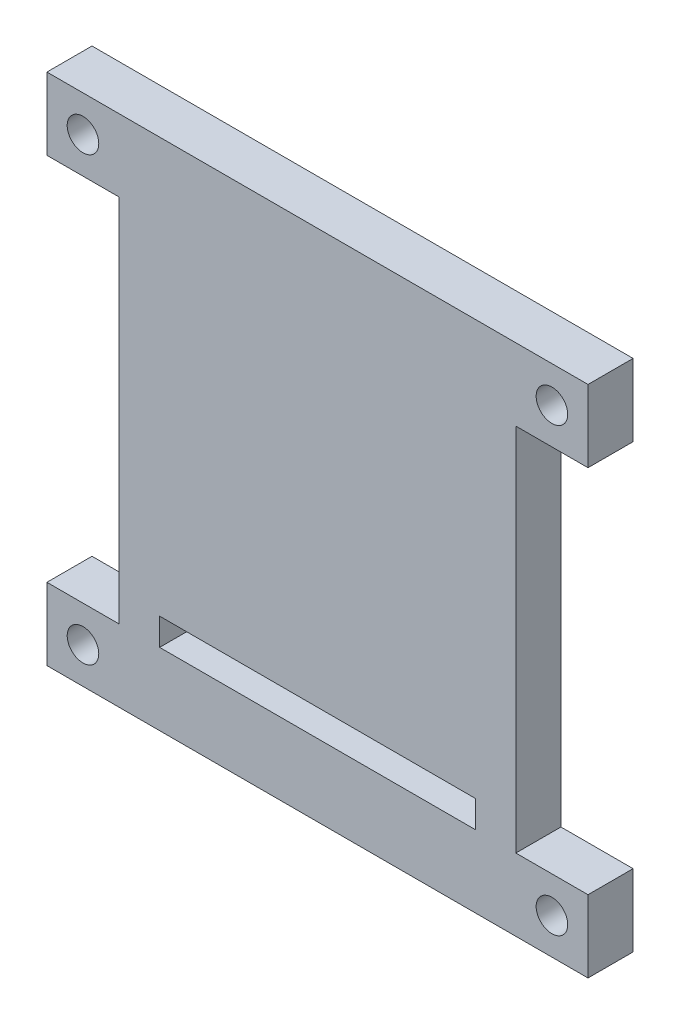
SolidWorks part; units mm, degrees
ref_plane "前基準面" through (0, 0, 0) normal (0, 0, 1) x (1, 0, 0)
ref_plane "上基準面" through (0, 0, 0) normal (0, 1, 0) x (1, 0, 0)
ref_plane "右基準面" through (0, 0, 0) normal (1, 0, 0) x (0, 0, -1)
sketch "草圖1" plane through (0, 0, 0) normal (0, 0, 1) x (1, 0, 0)
  line L1 (-22, 28.5) -> (22, 28.5)
  line L2 (-22, 28.5) -> (-22, -28.5)
  line L3 (-22, -28.5) -> (22, -28.5)
  line L4 (22, 28.5) -> (22, -28.5)
  line L5 (-22, 28.5) -> (22, -28.5) construction
  line L6 (-22, -28.5) -> (22, 28.5) construction
  line L7 (-30, 20.5) -> (-22, 20.5)
  line L8 (-30, 20.5) -> (-30, 28.5)
  line L9 (-30, 28.5) -> (-22, 28.5)
  line L10 (-22, 20.5) -> (-22, 28.5)
  line L11 (-30, 20.5) -> (-22, 28.5) construction
  line L12 (-30, 28.5) -> (-22, 20.5) construction
  line L13 (-30, -20.5) -> (-22, -20.5)
  line L14 (-30, -20.5) -> (-30, -28.5)
  line L15 (-30, -28.5) -> (-22, -28.5)
  line L16 (-22, -20.5) -> (-22, -28.5)
  line L17 (-30, -20.5) -> (-22, -28.5) construction
  line L18 (-30, -28.5) -> (-22, -20.5) construction
  line L19 (30, 20.5) -> (22, 20.5)
  line L20 (30, 20.5) -> (30, 28.5)
  line L21 (30, 28.5) -> (22, 28.5)
  line L22 (22, 20.5) -> (22, 28.5)
  line L23 (30, 20.5) -> (22, 28.5) construction
  line L24 (30, 28.5) -> (22, 20.5) construction
  line L25 (30, -20.5) -> (22, -20.5)
  line L26 (30, -20.5) -> (30, -28.5)
  line L27 (30, -28.5) -> (22, -28.5)
  line L28 (22, -20.5) -> (22, -28.5)
  line L29 (30, -20.5) -> (22, -28.5) construction
  line L30 (30, -28.5) -> (22, -20.5) construction
  circle A0 centre (-26, 24.5) radius 1.75
  circle A1 centre (26, 24.5) radius 1.75
  circle A2 centre (26, -24.5) radius 1.75
  circle A3 centre (-26, -24.5) radius 1.75
  point P0 (0, 0)
  point P6 (-26, 24.5)
  point P7 (-26, -24.5)
  point P11 (26, 24.5)
  point P15 (26, -24.5)
  dimension "D4" = 3.5
  dimension "D1" = 8
  dimension "D2" = 44
  dimension "D3" = 57
extrude "填料-伸長1" add sketch "草圖1" along normal blind 5 contours L9 L8 L7 L2 | L20 L21 L4 L19 | L27 L26 L25 L4 | L14 L15 L2 L13 | L4 L1 L2 L3
sketch "草圖2" plane through (0, 0, 5) normal (0, 0, 1) x (1, 0, 0)
  line L0 (0, -2.75) -> (0, 2.75) construction
  line L1 (-17.5, -17.5) -> (17.5, -17.5)
  line L2 (-17.5, -17.5) -> (-17.5, -20.5)
  line L3 (-17.5, -20.5) -> (17.5, -20.5)
  line L4 (17.5, -17.5) -> (17.5, -20.5)
  line L5 (-17.5, -17.5) -> (17.5, -20.5) construction
  line L6 (-17.5, -20.5) -> (17.5, -17.5) construction
  line L7 (30, -20.5) -> (22, -20.5) construction
  point P0 (0, -19)
  dimension "D1" = 3
  dimension "D2" = 35
extrude "除料-伸長1" cut sketch "草圖2" against normal up to next
